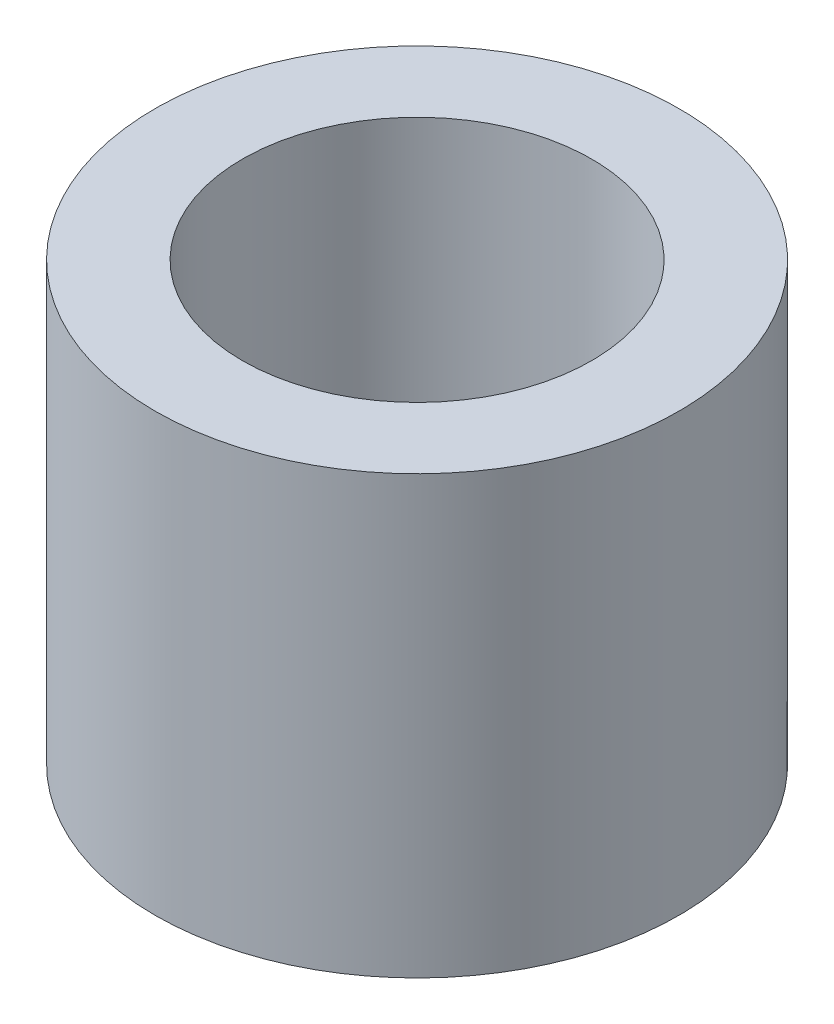
SolidWorks part; units mm, degrees
ref_plane "Front Plane" through (0, 0, 0) normal (0, 0, 1) x (1, 0, 0)
ref_plane "Top Plane" through (0, 0, 0) normal (0, 1, 0) x (1, 0, 0)
ref_plane "Right Plane" through (0, 0, 0) normal (1, 0, 0) x (0, 0, -1)
sketch "Sketch1" plane through (0, 0, 0) normal (0, 1, 0) x (1, 0, 0)
  circle A0 centre (0, 0) radius 2
  circle A1 centre (0, 0) radius 3
  dimension "D1" = 4
  dimension "D2" = 6
extrude "Boss-Extrude1" add sketch "Sketch1" along normal blind 5
